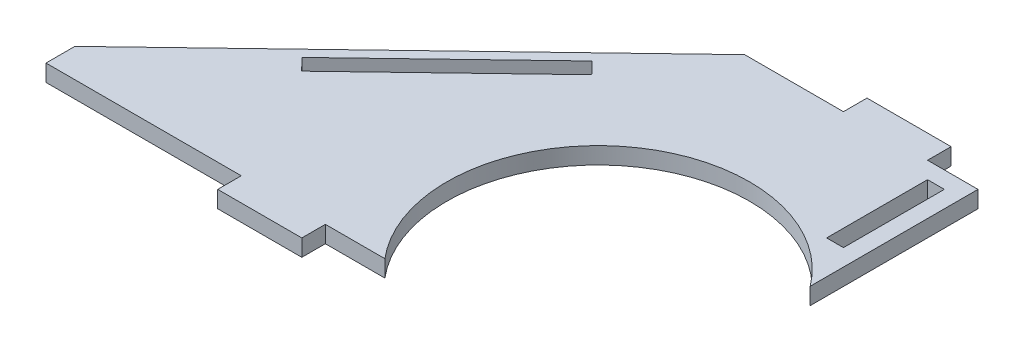
SolidWorks part; units mm, degrees
ref_plane "Front Plane" through (0, 0, 0) normal (0, 0, 1) x (1, 0, 0)
ref_plane "Top Plane" through (0, 0, 0) normal (0, 1, 0) x (1, 0, 0)
ref_plane "Right Plane" through (0, 0, 0) normal (1, 0, 0) x (0, 0, -1)
sketch "Sketch1" plane through (0, 0, 0) normal (0, 1, 0) x (1, 0, 0)
  line L1 (-23, -50) -> (2, -50)
  line L2 (-90, -43) -> (-90, 63)
  line L3 (50, 70) -> (75, 70)
  line L5 (19.6907, -43) -> (2, -43)
  line L6 (-90, -43) -> (-23, -43)
  line L8 (-23, -43) -> (-23, -50)
  line L9 (-23, -50) -> (2, -50)
  line L13 (2, -43) -> (2, -50)
  line L14 (90, 63) -> (90, 13.1328)
  line L15 (75, 63) -> (90, 63)
  line L16 (-90, 63) -> (50, 63)
  line L17 (50, 63) -> (50, 70)
  line L18 (50, 70) -> (75, 70)
  line L19 (75, 63) -> (75, 70)
  arc A9 (90, 13.1328) -> (19.6907, -43) centre (54.1, -14) ccw
  point P0 (0, 0)
  point P3 (54.1, -14)
  point P4 (54.1, -24)
  point P9 (54.1, -24)
  point P16 (0, 0)
  point P18 (0, 0)
  dimension "D4" = 140
  dimension "D5" = 106
  dimension "D6" = 90
  dimension "D1" = 25
  dimension "D2" = 7
  dimension "D3" = 120
  dimension "D7" = 43
  dimension "D11" = 7
  dimension "D12" = 7
  dimension "D13" = 25
  dimension "D14" = 67
  dimension "D15" = 90
extrude "Boss-Extrude1" add sketch "Sketch1" along normal blind 5
sketch "Sketch2" plane through (0, 5, 0) normal (0, 1, 0) x (1, 0, 0)
  line L0 (20.6461, 63) -> (-90, -43)
  line L3 (-90, 63) -> (50, 63) construction
  line L12 (90, 13.1328) -> (90, 63)
  line L13 (90, 63) -> (75, 63)
  line L14 (75, 63) -> (75, 70)
  line L15 (75, 70) -> (50, 70)
  line L16 (50, 70) -> (50, 63)
  line L17 (50, 63) -> (-90, 63)
  line L18 (-90, 63) -> (-90, -43)
  line L19 (-90, -43) -> (-23, -43)
  line L20 (-23, -43) -> (-23, -50)
  line L21 (-23, -50) -> (2, -50)
  line L22 (2, -50) -> (2, -43)
  line L23 (2, -43) -> (19.6907, -43)
  line L24 (90, 13.1328) -> (90, 63)
  line L25 (90, 63) -> (75, 63)
  line L26 (75, 63) -> (75, 70)
  line L27 (75, 70) -> (50, 70)
  line L28 (50, 70) -> (50, 63)
  line L29 (50, 63) -> (-90, 63)
  line L30 (-90, 63) -> (-90, -43)
  line L31 (-90, -43) -> (-23, -43)
  line L32 (-23, -43) -> (-23, -50)
  line L33 (-23, -50) -> (2, -50)
  line L34 (2, -50) -> (2, -43)
  line L41 (2, -43) -> (19.6907, -43)
  arc A1 (90, 13.1328) -> (19.6907, -43) centre (54.1, -14) ccw
  arc A6 (90, 13.1328) -> (19.6907, -43) centre (54.1, -14) ccw
  dimension "D1" = 0
extrude "Cut-Extrude1" cut sketch "Sketch2" against normal through all
sketch "Sketch4" plane through (0, 5, 0) normal (0, 1, 0) x (1, 0, 0)
  line L0 (-44.4257, -3.4939) -> (-1.0994, 38.0131)
  line L2 (-44.4257, -3.4939) -> (-40.9667, -7.1044)
  line L3 (2.3596, 34.4026) -> (-40.9667, -7.1044)
  line L5 (-0.3772, 38.7049) -> (3.0817, 35.0944)
  line L6 (-1.0994, 38.0131) -> (-0.3772, 38.7049)
  line L7 (2.3596, 34.4026) -> (3.0817, 35.0944)
  line L11 (50, 70) -> (50, 63)
  line L12 (50, 63) -> (20.6461, 63)
  line L13 (-90, -43) -> (-23, -43)
  line L14 (-23, -43) -> (-23, -50)
  line L15 (-23, -50) -> (2, -50)
  line L16 (2, -50) -> (2, -43)
  line L17 (2, -43) -> (19.6907, -43)
  line L18 (90, 13.1328) -> (90, 63)
  line L19 (90, 63) -> (75, 63)
  line L20 (75, 63) -> (75, 70)
  line L21 (75, 70) -> (50, 70)
  line L22 (50, 70) -> (50, 63)
  line L24 (-90, -43) -> (-23, -43)
  line L25 (-23, -43) -> (-23, -50)
  line L26 (-23, -50) -> (2, -50)
  line L27 (2, -50) -> (2, -43)
  line L29 (90, 13.1328) -> (90, 63)
  line L30 (90, 63) -> (75, 63)
  line L31 (75, 63) -> (75, 70)
  line L32 (75, 70) -> (50, 70)
  line L38 (50, 63) -> (20.6461, 63)
  line L39 (20.6461, 63) -> (-90, -43)
  line L45 (20.6461, 63) -> (-90, -43)
  line L48 (2, -43) -> (19.6907, -43)
  arc A1 (90, 13.1328) -> (19.6907, -43) centre (54.1, -14) ccw
  arc A6 (90, 13.1328) -> (19.6907, -43) centre (54.1, -14) ccw
  dimension "D2" = 3
  dimension "D3" = 5
  dimension "D4" = 5
  dimension "D5" = 60
  dimension "D6" = 1
  dimension "D1" = 0
extrude "Cut-Extrude2" cut sketch "Sketch4" against normal through all
sketch "Sketch6" plane through (0, 5, 0) normal (0, 1, 0) x (1, 0, 0)
  line L1 (80, 28) -> (85, 28)
  line L2 (80, 28) -> (80, 58)
  line L3 (80, 58) -> (85, 58)
  line L4 (85, 28) -> (85, 58)
  line L11 (50, 70) -> (50, 63)
  line L12 (50, 63) -> (20.6461, 63)
  line L13 (-90, -43) -> (-23, -43)
  line L14 (-23, -43) -> (-23, -50)
  line L15 (-23, -50) -> (2, -50)
  line L16 (2, -50) -> (2, -43)
  line L17 (2, -43) -> (19.6907, -43)
  line L18 (90, 13.1328) -> (90, 63)
  line L19 (90, 63) -> (75, 63)
  line L20 (75, 63) -> (75, 70)
  line L21 (75, 70) -> (50, 70)
  line L22 (50, 70) -> (50, 63)
  line L24 (-90, -43) -> (-23, -43)
  line L25 (-23, -43) -> (-23, -50)
  line L26 (-23, -50) -> (2, -50)
  line L27 (2, -50) -> (2, -43)
  line L29 (90, 13.1328) -> (90, 63)
  line L30 (90, 63) -> (75, 63)
  line L31 (75, 63) -> (75, 70)
  line L32 (75, 70) -> (50, 70)
  line L38 (50, 63) -> (20.6461, 63)
  line L39 (20.6461, 63) -> (-90, -43)
  line L41 (2, -43) -> (19.6907, -43)
  line L45 (20.6461, 63) -> (-90, -43)
  arc A1 (90, 13.1328) -> (19.6907, -43) centre (54.1, -14) ccw
  arc A6 (90, 13.1328) -> (19.6907, -43) centre (54.1, -14) ccw
  dimension "D2" = 5
  dimension "D3" = 5
  dimension "D4" = 30
  dimension "D5" = 5
  dimension "D1" = 0
extrude "Cut-Extrude4" cut sketch "Sketch6" against normal through all contours L1 L4 L3 L2
sketch "Sketch8" plane through (0, 5, 0) normal (0, 1, 0) x (1, 0, 0)
  line L0 (-81.0413, -34.4175) -> (-81.0413, -43)
  line L12 (50, 63) -> (20.6461, 63)
  line L13 (20.6461, 63) -> (-90, -43)
  line L14 (-90, -43) -> (-23, -43)
  line L15 (-23, -43) -> (-23, -50)
  line L16 (-23, -50) -> (2, -50)
  line L17 (2, -50) -> (2, -43)
  line L19 (90, 13.1328) -> (90, 63)
  line L20 (90, 63) -> (75, 63)
  line L21 (75, 63) -> (75, 70)
  line L22 (75, 70) -> (50, 70)
  line L23 (50, 70) -> (50, 63)
  line L24 (50, 63) -> (20.6461, 63)
  line L25 (20.6461, 63) -> (-90, -43)
  line L26 (-90, -43) -> (-23, -43)
  line L27 (-23, -43) -> (-23, -50)
  line L28 (-23, -50) -> (2, -50)
  line L29 (2, -50) -> (2, -43)
  line L31 (90, 13.1328) -> (90, 63)
  line L32 (90, 63) -> (75, 63)
  line L33 (75, 63) -> (75, 70)
  line L34 (75, 70) -> (50, 70)
  line L35 (50, 70) -> (50, 63)
  line L45 (2, -43) -> (19.6907, -43)
  line L46 (2, -43) -> (19.6907, -43)
  arc A1 (90, 13.1328) -> (19.6907, -43) centre (54.1, -14) ccw
  arc A5 (90, 13.1328) -> (19.6907, -43) centre (54.1, -14) ccw
  line M15 (20.6461, 63) -> (-90, -43)
  line M16 (-90, -43) -> (-23, -43)
  dimension "D1" = 0
extrude "Cut-Extrude5" cut sketch "Sketch8" against normal through all contours L0 M15 M16
